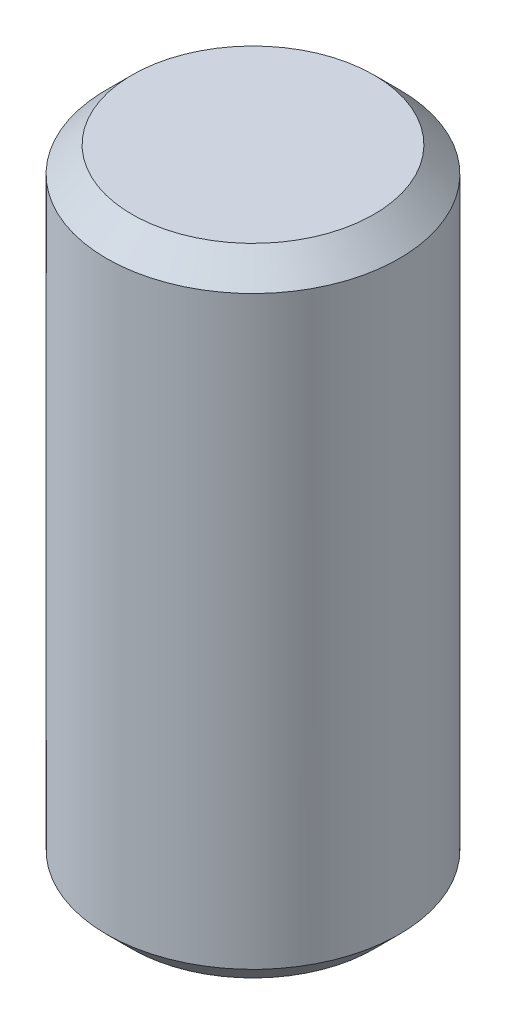
SolidWorks part; units mm, degrees
ref_plane "Front" through (0, 0, 0) normal (0, 0, 1) x (1, 0, 0)
ref_plane "Top" through (0, 0, 0) normal (0, 1, 0) x (1, 0, 0)
ref_plane "Right" through (0, 0, 0) normal (1, 0, 0) x (0, 0, -1)
sketch "Sketch1" plane through (0, 0, 0) normal (0, 0, 1) x (1, 0, 0)
  line L0 (0, 6.0802) -> (0, -6.0802) construction
  line L1 (0, -6.35) -> (2.921, -6.35)
  line L2 (2.921, -6.35) -> (2.921, 6.35)
  line L3 (2.921, 6.35) -> (0, 6.35)
  line L4 (0, 6.35) -> (0, -6.35)
  point P6 (0, 0)
  dimension "D1" = 5.842
  dimension "D2" = 12.7
revolve "Revolve1" add sketch "Sketch1" angle 360 about L0
chamfer "Chamfer1" distance 0.508 angle 45 2 edges at (0, -6.35, 2.921) (0, 6.35, 2.921)
